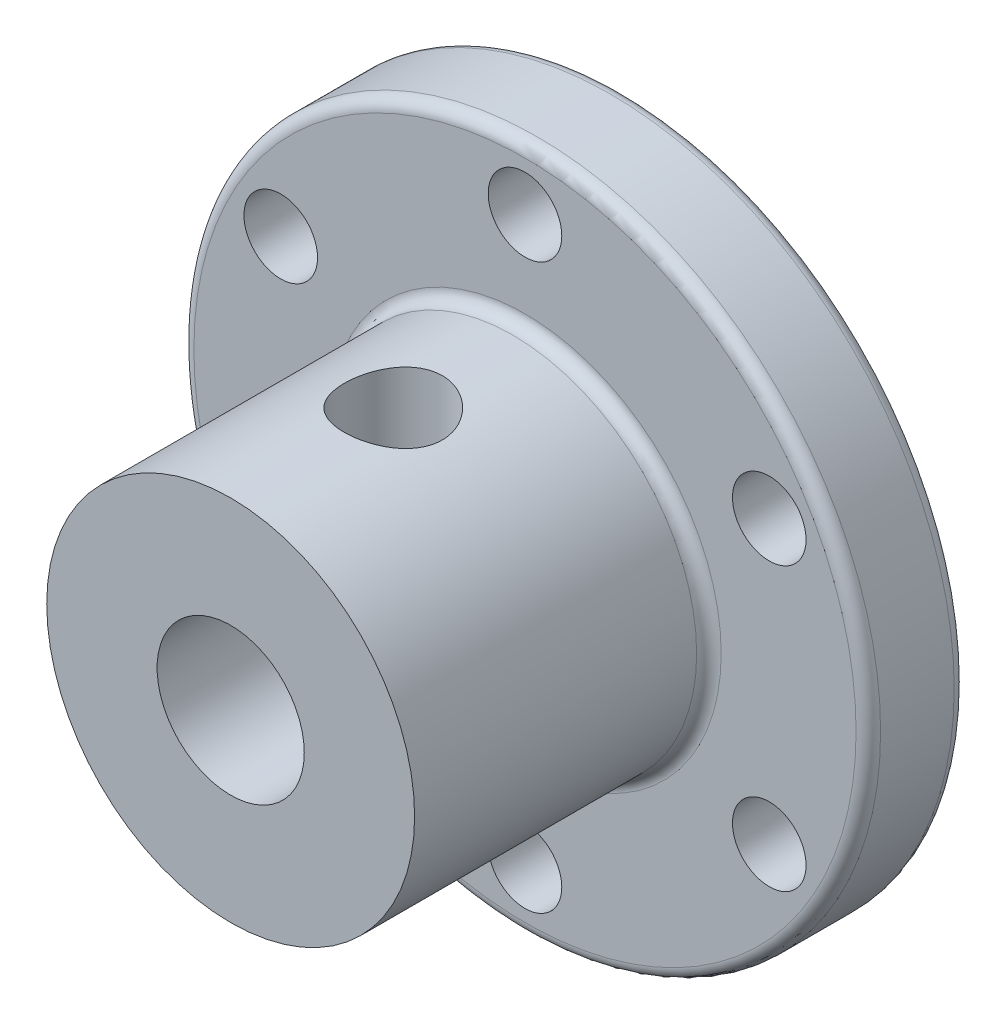
SolidWorks part; units mm, degrees
ref_plane "前视基准面" through (0, 0, 0) normal (0, 0, 1) x (1, 0, 0)
ref_plane "上视基准面" through (0, 0, 0) normal (0, 1, 0) x (1, 0, 0)
ref_plane "右视基准面" through (0, 0, 0) normal (1, 0, 0) x (0, 0, -1)
sketch "草图1" plane through (0, 0, 0) normal (0, 0, 1) x (1, 0, 0)
  circle A0 centre (0, 0) radius 14
  circle A1 centre (0, 0) radius 11.5 construction
  circle A2 centre (0, 11.5) radius 1.5
  circle A3 centre (9.9593, 5.75) radius 1.5
  circle A4 centre (9.9593, -5.75) radius 1.5
  circle A5 centre (0, -11.5) radius 1.5
  circle A6 centre (-9.9593, -5.75) radius 1.5
  circle A7 centre (-9.9593, 5.75) radius 1.5
  point P18 (0, 0)
  dimension "D1" = 28
  dimension "D2" = 23
  dimension "D3" = 6
extrude "凸台-拉伸1" add sketch "草图1" along normal blind 4
sketch "草图2" plane through (0, 0, 4) normal (0, 0, 1) x (1, 0, 0)
  circle A0 centre (0, 0) radius 7.5
  dimension "D1" = 15
extrude "凸台-拉伸2" add sketch "草图2" along normal blind 12
sketch "草图3" plane through (0, 0, 16) normal (0, 0, 1) x (1, 0, 0)
  circle A0 centre (0, 0) radius 3
extrude "切除-拉伸1" cut sketch "草图3" against normal through all
fillet "圆角1" radius 0.5 2 edges at (14, 0, 4) (14, 0, 0)
fillet "圆角2" radius 0.5 1 edges at (7.5, 0, 4)
sketch "草图4" plane through (0, 0, 0) normal (0, 1, 0) x (1, 0, 0)
  line L0 (0, -16) -> (0, 0) construction
  line L1 (-7.5, -16) -> (7.5, -16) construction
  circle A0 centre (0, -9.371) radius 2
extrude "切除-拉伸3" cut sketch "草图4" along normal through all
